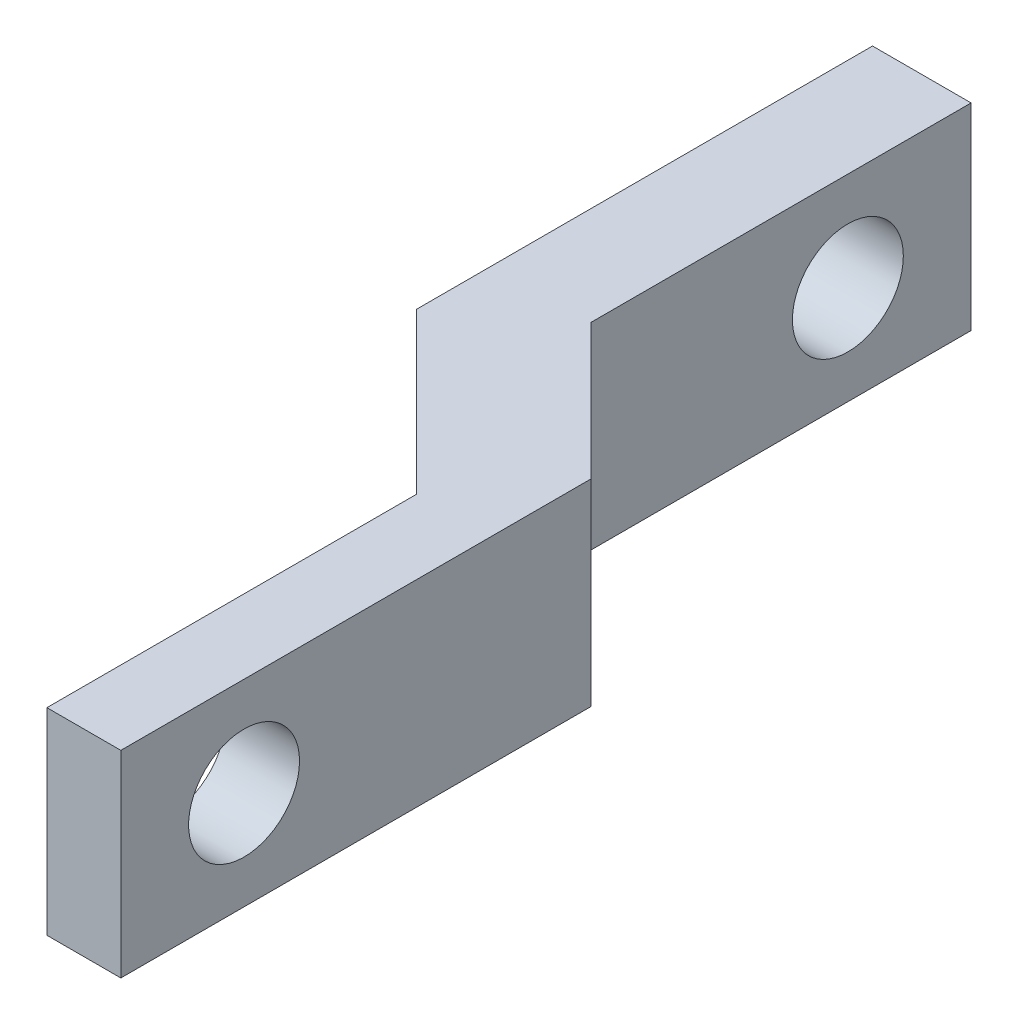
SolidWorks part; units mm, degrees
ref_plane "Front Plane" through (0, 0, 0) normal (0, 0, 1) x (1, 0, 0)
ref_plane "Top Plane" through (0, 0, 0) normal (0, 1, 0) x (1, 0, 0)
ref_plane "Right Plane" through (0, 0, 0) normal (1, 0, 0) x (0, 0, -1)
sketch "Sketch1" plane through (0, 0, 0) normal (0, 1, 0) x (1, 0, 0)
  line L0 (0, 0) -> (-3, 0)
  line L1 (-3, 0) -> (-3, 15)
  line L2 (-3, 15) -> (-9.5, 21.5)
  line L3 (-9.5, 21.5) -> (-9.5, 40)
  line L4 (-9.5, 40) -> (-5.5, 40)
  line L5 (-5.5, 40) -> (-5.5, 24.5711)
  line L6 (-5.5, 24.5711) -> (0, 19.0711)
  line L7 (0, 19.0711) -> (0, 0)
  dimension "D1" = 3
  dimension "D2" = 4
  dimension "D3" = 2.5
  dimension "D4" = 40
  dimension "D5" = 45
  dimension "D6" = 5
  dimension "D7" = 15
extrude "Boss-Extrude1" add sketch "Sketch1" along normal blind 8
sketch "Sketch2" plane through (-5.5, 0, 0) normal (1, 0, 0) x (0, 0, -1)
  line L0 (35, 4) -> (40, 4) construction
  line L2 (24.5711, 0) -> (40, 0) construction
  line L3 (40, 8) -> (40, 0) construction
  line L4 (24.5711, 8) -> (40, 8) construction
  line L5 (0, 8) -> (0, 0) construction
  line L6 (0, 0) -> (19.0711, 0) construction
  circle A0 centre (35, 4) radius 2.25
  circle A1 centre (5, 4) radius 2.25
  dimension "D1" = 4.5
  dimension "D2" = 4.5
  dimension "D5" = 5
  dimension "D6" = 4
  dimension "D3" = 4
  dimension "D4" = 5
extrude "Cut-Extrude1" cut sketch "Sketch2" against normal through all and the other way through all
